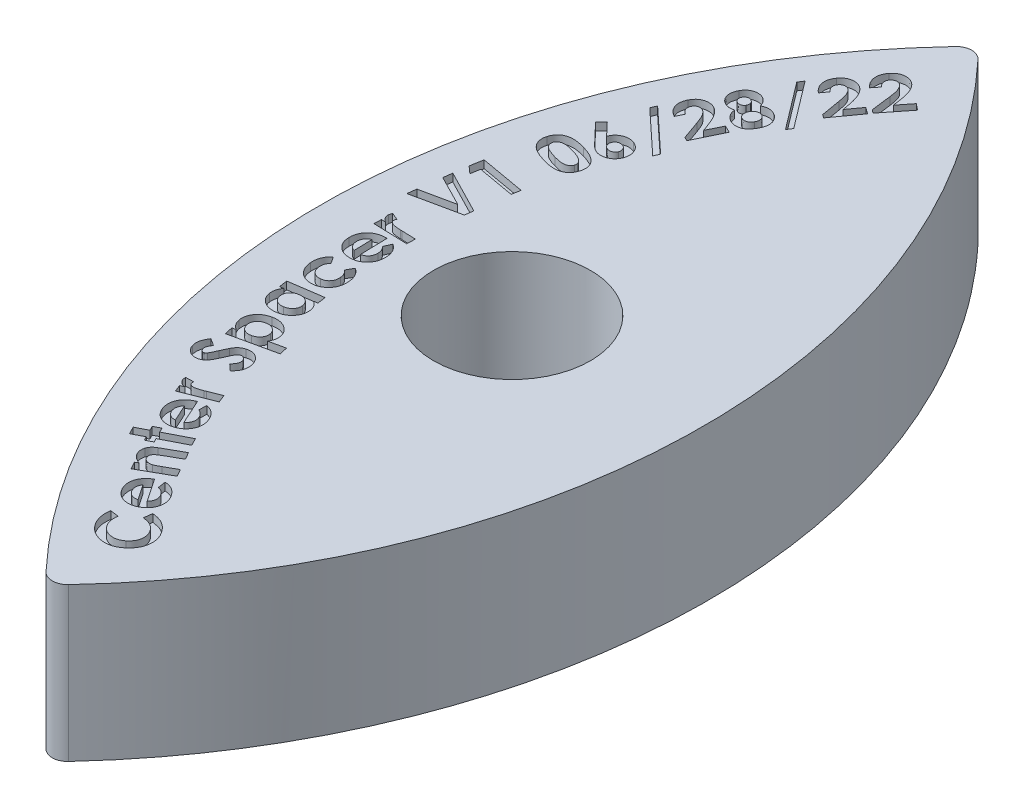
SolidWorks part; units mm, degrees
ref_plane "Front Plane" through (0, 0, 0) normal (0, 0, 1) x (1, 0, 0)
ref_plane "Top Plane" through (0, 0, 0) normal (0, 1, 0) x (1, 0, 0)
ref_plane "Right Plane" through (0, 0, 0) normal (1, 0, 0) x (0, 0, -1)
sketch "Sketch2" plane through (0, 0, 0) normal (1, 0, 0) x (0, 0, -1)
  line L0 (-15.7391, 19.787) -> (12.7788, 17.9806) construction
  line L1 (-38.1, 0) -> (-38.1, 12.7)
  line L2 (-38.1, 12.7) -> (38.1, 12.7)
  line L3 (38.1, 12.7) -> (38.1, -0.5365)
  line L4 (-38.1, 0) -> (38.1, 0) construction
  line L5 (-302.918, -43.2315) -> (-283.9965, -45.4399) construction
  line L6 (-13.828, 3.2133) -> (5.1982, 4.1648) construction
  spline S0 degree 2 poles (-38.1, 0) (0.0038, 0.2682) (38.1, -0.5365) knots 0 0 0 1 1 1
  point P4 (0, -3.7491)
  dimension "D1" = 28.575
  dimension "D2" = 12.7
  dimension "D3" = 19.05
  dimension "D4" = 76.2
  dimension "D5" = 19.05
extrude "Boss-Extrude1" add sketch "Sketch2" against normal mid plane 31.75
sketch "Sketch3" plane through (0, 12.7, 0) normal (0, 1, 0) x (1, 0, 0)
  line L0 (-15.875, 38.1) -> (-15.875, -38.1) construction
  line L1 (0, 0) -> (0, 38.1) construction
  line L2 (-15.875, 38.1) -> (15.875, 38.1) construction
  line L3 (15.875, 38.1) -> (15.875, -38.1) construction
  line L4 (-15.875, -38.1) -> (15.875, -38.1) construction
  line L9 (15.875, -38.1) -> (15.875, 38.1)
  line L10 (15.875, 38.1) -> (-15.875, 38.1)
  line L11 (-15.875, 38.1) -> (-15.875, -38.1)
  line L12 (-15.875, -38.1) -> (15.875, -38.1)
  line L13 (15.875, -38.1) -> (15.875, 38.1)
  line L14 (15.875, 38.1) -> (-15.875, 38.1)
  line L15 (-15.875, 38.1) -> (-15.875, -38.1)
  line L16 (-15.875, -38.1) -> (15.875, -38.1)
  arc A0 (-0.9249, 37.7004) -> (-0.9249, -37.7004) centre (39.1353, 0) ccw
  arc A1 (0.9249, 37.7004) -> (0.9249, -37.7004) centre (-39.1353, 0) cw
  arc A2 (0.9249, 37.7004) -> (-0.9249, 37.7004) centre (0, 36.83) ccw
  arc A3 (0.9249, -37.7004) -> (-0.9249, -37.7004) centre (0, -36.83) cw
  circle A4 centre (0, 0) radius 6.5
  dimension "D1" = 1.27
  dimension "D3" = 13
  dimension "D2" = 0
extrude "Cut-Extrude1" cut sketch "Sketch3" against normal through all
sketch "Sketch5" plane through (0, 12.7, 0) normal (0, 1, 0) x (1, 0, 0)
  arc A2 (3.6994, 33.3485) -> (3.6994, -33.3485) centre (39.1353, 0) ccw
  arc A3 (3.6138, 33.2573) -> (3.6994, -33.3485) centre (39.1353, 0) ccw
  dimension "D1" = 6.35
sketch "Sketch6" plane through (0, 12.7, 0) normal (0, 1, 0) x (1, 0, 0)
  text T0 "<b>Center Spacer V1 06/28/22</b>" font "Century Gothic" height 3.81
extrude "Cut-Extrude2" cut sketch "Sketch6" against normal blind 0.635
